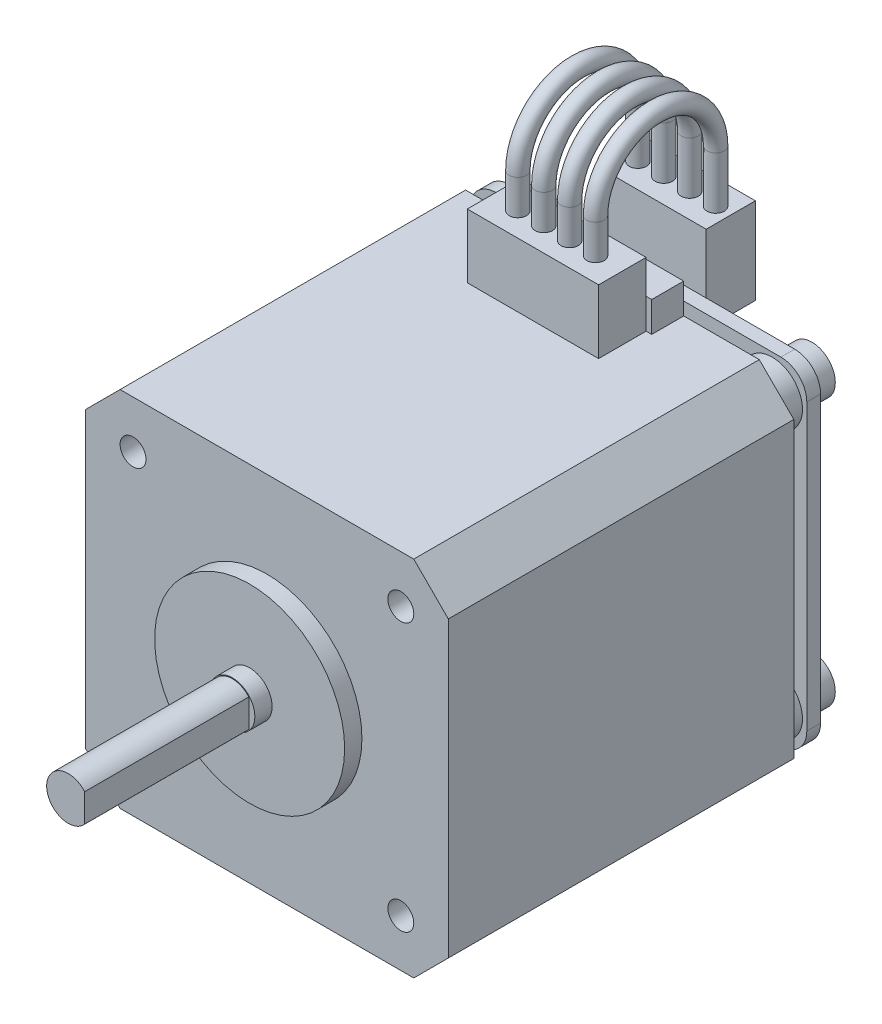
SolidWorks part; units mm, degrees
ref_plane "Front Plane" through (0, 0, 0) normal (0, 0, 1) x (1, 0, 0)
ref_plane "Top Plane" through (0, 0, 0) normal (0, 1, 0) x (1, 0, 0)
ref_plane "Right Plane" through (0, 0, 0) normal (1, 0, 0) x (0, 0, -1)
sketch "Sketch1" plane through (0, 0, 0) normal (0, 0, 1) x (1, 0, 0)
  circle A0 centre (0, 0) radius 11
  dimension "D1" = 22
extrude "Boss-Extrude1" add sketch "Sketch1" along normal blind 2
sketch "Sketch2" plane through (0, 0, 2) normal (0, 0, 1) x (1, 0, 0)
  circle A0 centre (0, 0) radius 2.6
  dimension "D1" = 5.2
extrude "Boss-Extrude2" add sketch "Sketch2" along normal blind 21
sketch "Sketch3" plane through (0, 0, 23) normal (0, 0, 1) x (1, 0, 0)
  line L0 (1.9, 1.7748) -> (1.9, -1.7748)
  circle A0 centre (0, 0) radius 2.6 construction
  arc A1 (1.9, -1.7748) -> (1.9, 1.7748) centre (0, 0) ccw
  circle A2 centre (0, 0) radius 2.6 construction
  dimension "D1" = 4.5
extrude "Cut-Extrude1" cut sketch "Sketch3" against normal blind 19
sketch "Sketch4" plane through (0, 0, 0) normal (0, 0, -1) x (-1, 0, 0)
  line L1 (-21, -21) -> (21, -21)
  line L2 (-21, -21) -> (-21, 21)
  line L3 (-21, 21) -> (21, 21)
  line L4 (21, -21) -> (21, 21)
  line L5 (-21, -21) -> (21, 21) construction
  line L6 (-21, 21) -> (21, -21) construction
  point P0 (0, 0)
  dimension "D1" = 42
extrude "Boss-Extrude3" add sketch "Sketch4" along normal blind 40
chamfer "Chamfer1" distance 4 angle 45 4 edges at (21, 21, -20) (-21, -21, -20) (-21, 21, -20) (21, -21, -20)
sketch "Sketch5" plane through (0, 0, -40) normal (0, 0, -1) x (-1, 0, 0)
  line L1 (-15.5, -15.5) -> (15.5, -15.5)
  line L2 (-15.5, -15.5) -> (-15.5, 15.5)
  line L3 (-15.5, 15.5) -> (15.5, 15.5)
  line L4 (15.5, -15.5) -> (15.5, 15.5)
  line L5 (-15.5, -15.5) -> (15.5, 15.5) construction
  line L6 (-15.5, 15.5) -> (15.5, -15.5) construction
  circle A0 centre (-15.5, 15.5) radius 1.5
  circle A1 centre (15.5, 15.5) radius 1.5
  circle A2 centre (15.5, -15.5) radius 1.5
  circle A3 centre (-15.5, -15.5) radius 1.5
  point P0 (0, 0)
  dimension "D2" = 3
  dimension "D1" = 31
extrude "Cut-Extrude2" cut sketch "Sketch5" against normal through all contours L3 A0 L2 | L2 A0 L3 | L4 A1 L3 | L3 A1 L4 | L1 A2 L4 | L4 A2 L1 | L2 A3 L1 | L1 A3 L2
sketch "Sketch6" plane through (0, 0, -40) normal (0, 0, -1) x (-1, 0, 0)
  circle A0 centre (-15.5, 15.5) radius 3.5
  circle A1 centre (15.5, 15.5) radius 3.5
  circle A2 centre (15.5, -15.5) radius 3.5
  circle A3 centre (-15.5, -15.5) radius 3.5
  dimension "D1" = 7
extrude "Boss-Extrude4" add sketch "Sketch6" along normal blind 3
sketch "Sketch7" plane through (0, 0, -43) normal (0, 0, -1) x (-1, 0, 0)
  line L1 (-19.5, -19.5) -> (19.5, -19.5)
  line L2 (-19.5, -19.5) -> (-19.5, 19.5)
  line L3 (-19.5, 19.5) -> (19.5, 19.5)
  line L4 (19.5, -19.5) -> (19.5, 19.5)
  line L5 (-19.5, -19.5) -> (19.5, 19.5) construction
  line L6 (-19.5, 19.5) -> (19.5, -19.5) construction
  point P0 (0, 0)
  dimension "D1" = 39
extrude "Boss-Extrude5" add sketch "Sketch7" along normal blind 1.6
fillet "Fillet1" radius 3 4 edges at (19.5, -19.5, -43.8) (-19.5, -19.5, -43.8) (-19.5, 19.5, -43.8) (19.5, 19.5, -43.8)
sketch "Sketch8" plane through (0, 0, -40) normal (0, 0, -1) x (-1, 0, 0)
  line L0 (17, 21) -> (-17, 21) construction
  line L1 (-8.25, 17.5) -> (8.25, 17.5)
  line L2 (-8.25, 17.5) -> (-8.25, 24.5)
  line L3 (-8.25, 24.5) -> (8.25, 24.5)
  line L4 (8.25, 17.5) -> (8.25, 24.5)
  line L5 (-8.25, 17.5) -> (8.25, 24.5) construction
  line L6 (-8.25, 24.5) -> (8.25, 17.5) construction
  point P0 (0, 21)
  dimension "D1" = 16.5
  dimension "D2" = 3.5
extrude "Boss-Extrude6" add sketch "Sketch8" against normal blind 3.7
sketch "Sketch9" plane through (0, 21, 0) normal (0, 1, 0) x (1, 0, 0)
  line L0 (0, 0) -> (0, 36.3) construction
  line L1 (8.25, 36.3) -> (-8.25, 36.3) construction
  line L2 (-8.25, 36.3) -> (8.25, 36.3) construction
  line L3 (-7.6, 36.3) -> (7.6, 36.3)
  line L4 (-7.6, 36.3) -> (-7.6, 30.8)
  line L5 (-7.6, 30.8) -> (7.6, 30.8)
  line L6 (7.6, 36.3) -> (7.6, 30.8)
  line L7 (-7.6, 36.3) -> (7.6, 30.8) construction
  line L8 (-7.6, 30.8) -> (7.6, 36.3) construction
  point P5 (0, 33.55)
  dimension "D1" = 5.5
  dimension "D2" = 15.2
extrude "Boss-Extrude7" add sketch "Sketch9" along normal blind 7.4
sketch "Sketch10" plane through (0, 0, -44.6) normal (0, 0, -1) x (-1, 0, 0)
  line L0 (0, 0) -> (0, 19.5) construction
  line L1 (16.5, 19.5) -> (-16.5, 19.5) construction
  line L2 (-7.6, 28.4) -> (7.6, 28.4) construction
  line L3 (-6.25, 16.4) -> (6.25, 16.4)
  line L4 (-6.25, 16.4) -> (-6.25, 26.4)
  line L5 (-6.25, 26.4) -> (6.25, 26.4)
  line L6 (6.25, 16.4) -> (6.25, 26.4)
  line L7 (-6.25, 16.4) -> (6.25, 26.4) construction
  line L8 (-6.25, 26.4) -> (6.25, 16.4) construction
  point P5 (0, 21.4)
  dimension "D1" = 10
  dimension "D2" = 12.5
  dimension "D3" = 2
extrude "Boss-Extrude8" add sketch "Sketch10" along normal blind 5.7
sketch "Sketch11" plane through (0, 26.4, 0) normal (0, 1, 0) x (1, 0, 0)
  line L0 (-6.25, 47.45) -> (6.25, 47.45) construction
  line L1 (-6.25, 50.3) -> (-6.25, 44.6) construction
  line L2 (6.25, 50.3) -> (6.25, 44.6) construction
  line L3 (-4.5, 47.45) -> (-4.5, 44.6) construction
  line L4 (-6.25, 44.6) -> (6.25, 44.6) construction
  line L5 (-1.5, 47.45) -> (-1.5, 44.6) construction
  line L6 (-6.25, 44.6) -> (6.25, 44.6) construction
  line L7 (1.5, 47.45) -> (1.5, 44.6) construction
  line L8 (4.5, 47.45) -> (4.5, 44.6) construction
  line L9 (-4.5, 46.025) -> (-1.5, 46.025) construction
  line L10 (-1.5, 46.025) -> (1.5, 46.025) construction
  line L11 (1.5, 46.025) -> (4.5, 46.025) construction
  line L12 (-6.25, 50.3) -> (-4.5, 47.45) construction
  line L13 (6.25, 50.3) -> (4.5, 47.45) construction
  circle A0 centre (-4.5, 47.45) radius 1
  circle A1 centre (-1.5, 47.45) radius 1
  circle A2 centre (1.5, 47.45) radius 1
  circle A3 centre (4.5, 47.45) radius 1
  dimension "D1" = 2
  dimension "D2" = 9
sketch "Sketch12" plane through (0, 0, 0) normal (1, 0, 0) x (0, 0, -1)
  line L0 (33.55, 28.4) -> (33.55, 24.0981) construction
  line L1 (30.8, 28.4) -> (36.3, 28.4) construction
  line L2 (47.45, 26.4) -> (47.45, 22.93) construction
  line L3 (48.45, 26.4) -> (46.45, 26.4) construction
  line L4 (33.55, 28.4) -> (33.55, 32.45)
  line L5 (47.45, 32.45) -> (47.45, 26.4)
  arc A0 (33.55, 32.45) -> (47.45, 32.45) centre (40.5, 32.45) cw
  dimension "D1" = 11
sweep "Sweep1" add profiles "Sketch11" path "Sketch12"
sketch "Sketch13" plane through (0, 0, -44.6) normal (0, 0, -1) x (-1, 0, 0)
  circle A0 centre (-15.5, -15.5) radius 1.5 construction
  circle A1 centre (15.5, -15.5) radius 1.5 construction
  circle A2 centre (15.5, 15.5) radius 1.5 construction
  circle A3 centre (-15.5, 15.5) radius 1.5 construction
  circle A4 centre (-15.5, -15.5) radius 1.5 construction
  circle A5 centre (15.5, -15.5) radius 1.5 construction
  circle A6 centre (15.5, 15.5) radius 1.5 construction
  circle A7 centre (-15.5, 15.5) radius 1.5 construction
  circle A8 centre (-15.5, 15.5) radius 2.7
  circle A9 centre (15.5, 15.5) radius 2.7
  circle A10 centre (-15.5, -15.5) radius 2.7
  circle A11 centre (15.5, -15.5) radius 2.7
  dimension "D2" = 1.2
  dimension "D1" = 1.2
  dimension "D3" = 1.2
  dimension "D4" = 1.2
extrude "Boss-Extrude9" add sketch "Sketch13" along normal blind 3
sketch "Sketch14" plane through (0, 0, -44.6) normal (0, 0, -1) x (-1, 0, 0)
  line L1 (-6, -5) -> (6, -5)
  line L2 (-6, -5) -> (-6, 5)
  line L3 (-6, 5) -> (6, 5)
  line L4 (6, -5) -> (6, 5)
  line L5 (-6, -5) -> (6, 5) construction
  line L6 (-6, 5) -> (6, -5) construction
  point P0 (0, 0)
  dimension "D1" = 10
  dimension "D2" = 12
extrude "Boss-Extrude10" add sketch "Sketch14" along normal blind 2
sketch "Sketch15" plane through (0, 0, -44.6) normal (0, 0, -1) x (-1, 0, 0)
  line L0 (-19.5, -17.5) -> (19.5, -17.5) construction
  line L1 (-19.5, 16.5) -> (-19.5, -16.5) construction
  line L2 (19.5, -16.5) -> (19.5, 16.5) construction
  line L3 (0, -17.5) -> (0, 0) construction
  line L4 (-10.5, -19) -> (-5.5, -19)
  line L5 (-10.5, -19) -> (-10.5, -16)
  line L6 (-10.5, -16) -> (-5.5, -16)
  line L7 (-5.5, -19) -> (-5.5, -16)
  line L8 (-10.5, -19) -> (-5.5, -16) construction
  line L9 (-10.5, -16) -> (-5.5, -19) construction
  line L10 (-2.5, -19) -> (2.5, -19)
  line L11 (-2.5, -19) -> (-2.5, -16)
  line L12 (-2.5, -16) -> (2.5, -16)
  line L13 (2.5, -19) -> (2.5, -16)
  line L14 (-2.5, -19) -> (2.5, -16) construction
  line L15 (-2.5, -16) -> (2.5, -19) construction
  line L16 (5.5, -19) -> (10.5, -19)
  line L17 (5.5, -19) -> (5.5, -16)
  line L18 (5.5, -16) -> (10.5, -16)
  line L19 (10.5, -19) -> (10.5, -16)
  line L20 (5.5, -19) -> (10.5, -16) construction
  line L21 (5.5, -16) -> (10.5, -19) construction
  line L22 (0, 0) -> (-8, -17.5) construction
  line L23 (0, 0) -> (8, -17.5) construction
  line L24 (-17, -21) -> (17, -21) construction
  point P6 (-8, -17.5)
  point P11 (0, -17.5)
  point P16 (8, -17.5)
  dimension "D1" = 5
  dimension "D2" = 3
  dimension "D3" = 3.5
  dimension "D4" = 8
extrude "Boss-Extrude11" add sketch "Sketch15" along normal blind 4
sketch "Sketch16" plane through (0, 0, -44.6) normal (0, 0, -1) x (-1, 0, 0)
  line L0 (0, 0) -> (34.9064, 0) construction
  line L1 (21, -17) -> (21, 17) construction
  line L2 (16.8, -8.75) -> (24, -8.75)
  line L3 (16.8, -8.75) -> (16.8, 8.75)
  line L4 (16.8, 8.75) -> (24, 8.75)
  line L5 (24, -8.75) -> (24, 8.75)
  line L6 (16.8, -8.75) -> (24, 8.75) construction
  line L7 (16.8, 8.75) -> (24, -8.75) construction
  point P3 (20.4, 0)
  dimension "D1" = 7.2
  dimension "D2" = 17.5
  dimension "D3" = 3
extrude "Boss-Extrude12" add sketch "Sketch16" along normal up to surface (5.7 mm away) up to face at (0, 21.4, -50.3)
sketch "Sketch17" plane through (0, 0, 23) normal (0, 0, 1) x (1, 0, 0)
  circle A0 centre (0, 0) radius 2.5
  circle A1 centre (0, 0) radius 3.1997
  dimension "D1" = 5
extrude "Cut-Extrude3" cut sketch "Sketch17" against normal up to surface (19 mm away) up to face at (2.25, 0, 4)
